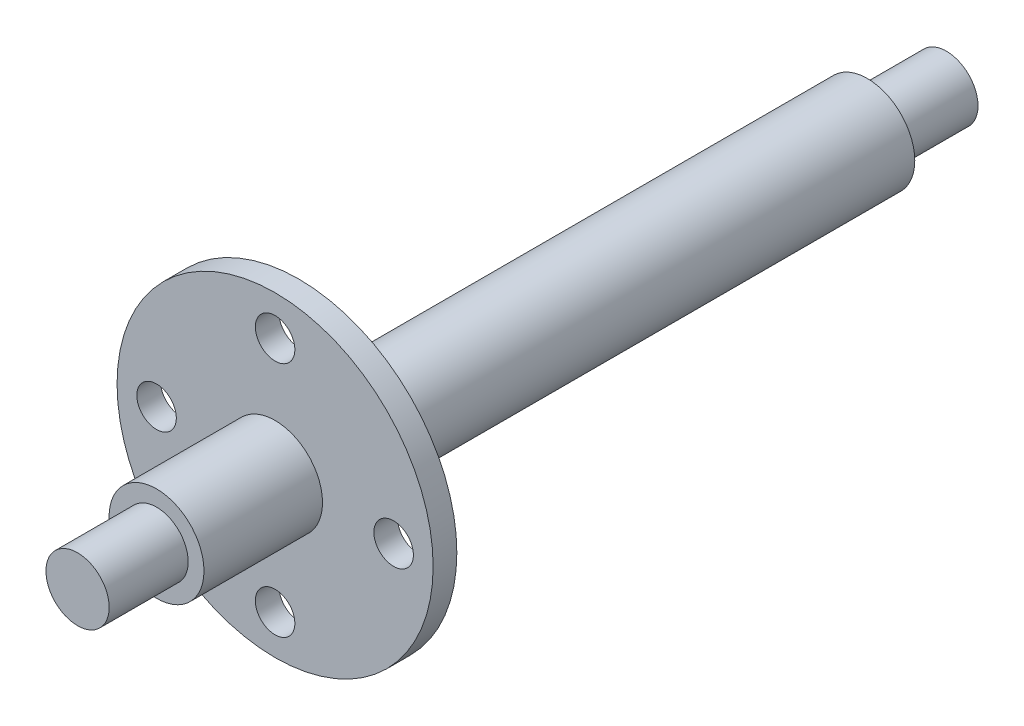
SolidWorks part; units mm, degrees
material "6061 Alloy"
ref_plane "Front Plane" through (0, 0, 0) normal (0, 0, 1) x (1, 0, 0)
ref_plane "Top Plane" through (0, 0, 0) normal (0, 1, 0) x (1, 0, 0)
ref_plane "Right Plane" through (0, 0, 0) normal (1, 0, 0) x (0, 0, -1)
sketch "Sketch1" plane through (0, 0, 0) normal (0, 0, 1) x (1, 0, 0)
  circle A0 centre (0, 0) radius 6
  dimension "D1" = 12
extrude "Boss-Extrude1" add sketch "Sketch1" along normal blind 109.95
ref_plane "Plane1" through (0, 0, 81.95) normal (0, 0, 1) x (1, 0, 0)
sketch "Sketch2" plane through (0, 0, 81.95) normal (0, 0, 1) x (1, 0, 0)
  circle A0 centre (0, 0) radius 20
  circle A1 centre (0, 0) radius 15 construction
  circle A2 centre (0, 15) radius 2.5
  circle A3 centre (15, 0) radius 2.5
  circle A4 centre (0, -15) radius 2.5
  circle A5 centre (-15, 0) radius 2.5
  point P15 (0, 0)
  dimension "D1" = 40
  dimension "D2" = 30
  dimension "D3" = 5
  dimension "D4" = 4
extrude "Boss-Extrude2" add sketch "Sketch2" along normal blind 3
sketch "Sketch3" plane through (0, 0, 109.95) normal (0, 0, 1) x (1, 0, 0)
  circle A0 centre (0, 0) radius 4
  circle A1 centre (0, 0) radius 6
  dimension "D1" = 8
  dimension "D2" = 12
extrude "Cut-Extrude1" cut sketch "Sketch3" against normal blind 10
ref_plane "Plane2" through (0, 0, 54.975) normal (0, 0, 1) x (1, 0, 0)
mirror "Mirror1" about plane through (0, 0, 54.975) normal (0, 0, 1) of "Cut-Extrude1"
